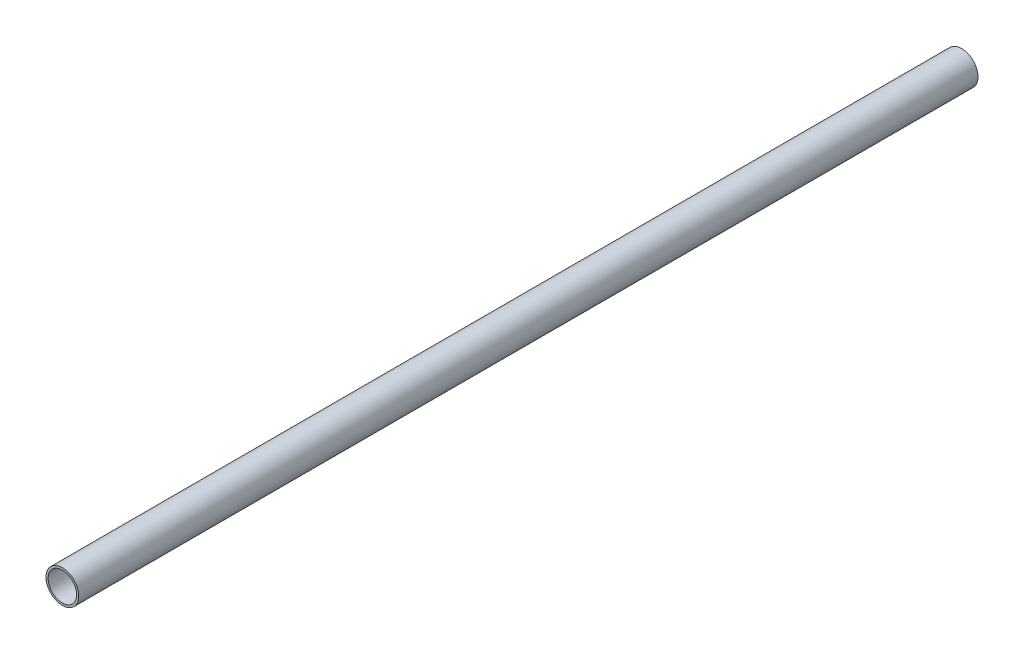
SolidWorks part; units mm, degrees
ref_plane "Front Plane" through (0, 0, 0) normal (0, 0, 1) x (1, 0, 0)
ref_plane "Top Plane" through (0, 0, 0) normal (0, 1, 0) x (1, 0, 0)
ref_plane "Right Plane" through (0, 0, 0) normal (1, 0, 0) x (0, 0, -1)
sketch "Sketch1" plane through (0, 0, 0) normal (0, 0, 1) x (1, 0, 0)
  circle A0 centre (0, 0) radius 38.6334
  circle A1 centre (0, 0) radius 44.45
  point P2 (0, -1.4675)
  dimension "D1" = 77.2668
  dimension "D2" = 88.9
extrude "Boss-Extrude1" add sketch "Sketch1" along normal mid plane 2438.4
